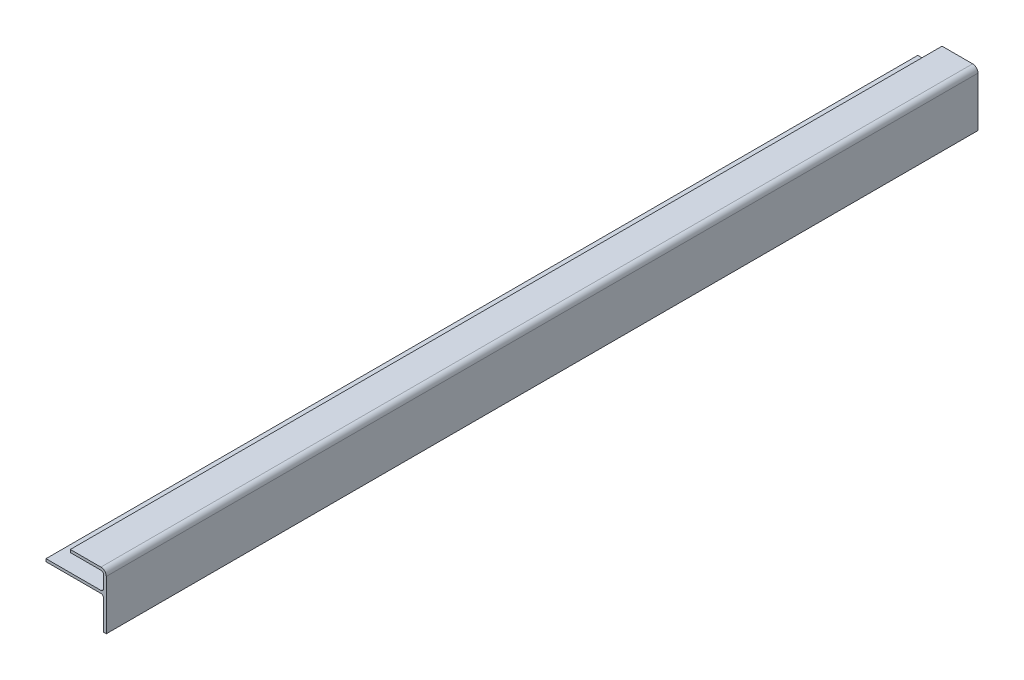
SolidWorks part; units mm, degrees
material "Pure Lead"
ref_plane "Front Plane" through (0, 0, 0) normal (0, 0, 1) x (1, 0, 0)
ref_plane "Top Plane" through (0, 0, 0) normal (0, 1, 0) x (1, 0, 0)
ref_plane "Right Plane" through (0, 0, 0) normal (1, 0, 0) x (0, 0, -1)
sketch "Sketch1" plane through (0, 0, 0) normal (0, 0, 1) x (1, 0, 0)
  line L0 (1219.2, 19.05) -> (1219.2, 36.5125)
  line L1 (1217.6125, 38.1) -> (1185.2275, 38.1)
  line L2 (1220.7875, 48.387) -> (1220.7875, 19.05)
  line L3 (1217.6125, 51.562) -> (1199.5785, 51.562)
  line L4 (1199.5785, 49.9745) -> (1217.6125, 49.9745)
  line L5 (1219.2, 48.387) -> (1219.2, 41.275)
  line L6 (1185.2275, 39.6875) -> (1217.6125, 39.6875)
  line L7 (1199.5785, 51.562) -> (1199.5785, 49.9745)
  line L9 (1185.2275, 38.1) -> (1185.2275, 39.6875)
  line L10 (1219.2, 19.05) -> (1220.7875, 19.05)
  arc A0 (1219.2, 36.5125) -> (1217.6125, 38.1) centre (1217.6125, 36.5125) ccw
  arc A1 (1220.7875, 48.387) -> (1217.6125, 51.562) centre (1217.6125, 48.387) ccw
  arc A2 (1219.2, 48.387) -> (1217.6125, 49.9745) centre (1217.6125, 48.387) ccw
  arc A3 (1217.6125, 39.6875) -> (1219.2, 41.275) centre (1217.6125, 41.275) ccw
extrude "Extrude1" add sketch "Sketch1" along normal mid plane 514.35
